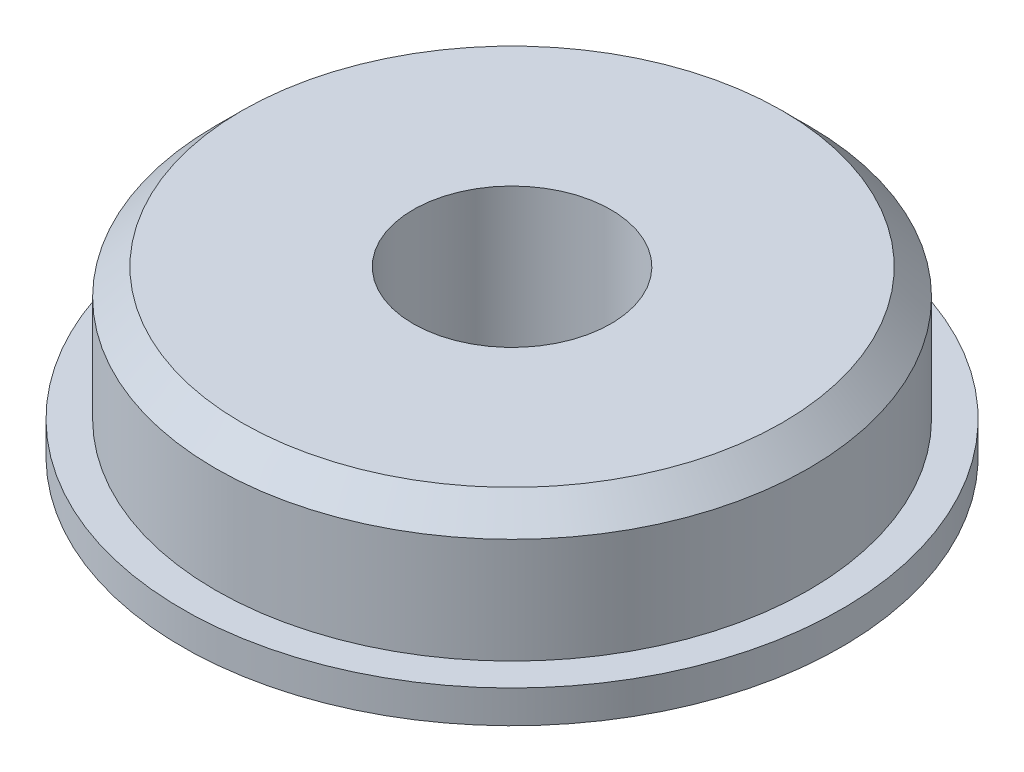
SolidWorks part; units mm, degrees
ref_plane "Front Plane" through (0, 0, 0) normal (0, 0, 1) x (1, 0, 0)
ref_plane "Top Plane" through (0, 0, 0) normal (0, 1, 0) x (1, 0, 0)
ref_plane "Right Plane" through (0, 0, 0) normal (1, 0, 0) x (0, 0, -1)
sketch "Sketch1" plane through (0, 0, 0) normal (0, 1, 0) x (1, 0, 0)
  circle A0 centre (0, 0) radius 14.2875
  circle A1 centre (0, 0) radius 4.7625
  dimension "D1" = 28.575
  dimension "D2" = 9.525
extrude "Boss-Extrude1" add sketch "Sketch1" along normal blind 7.9248
sketch "Sketch2" plane through (0, 0, 0) normal (0, -1, 0) x (1, 0, 0)
  circle A0 centre (0, 0) radius 15.875
  circle A2 centre (0, 0) radius 14.2875
  dimension "D1" = 31.75
  dimension "D2" = 28.575
extrude "Boss-Extrude2" add sketch "Sketch2" against normal blind 1.5748
chamfer "Chamfer1" distance 1.27 angle 45 1 edges at (0, 7.9248, 14.2875)
